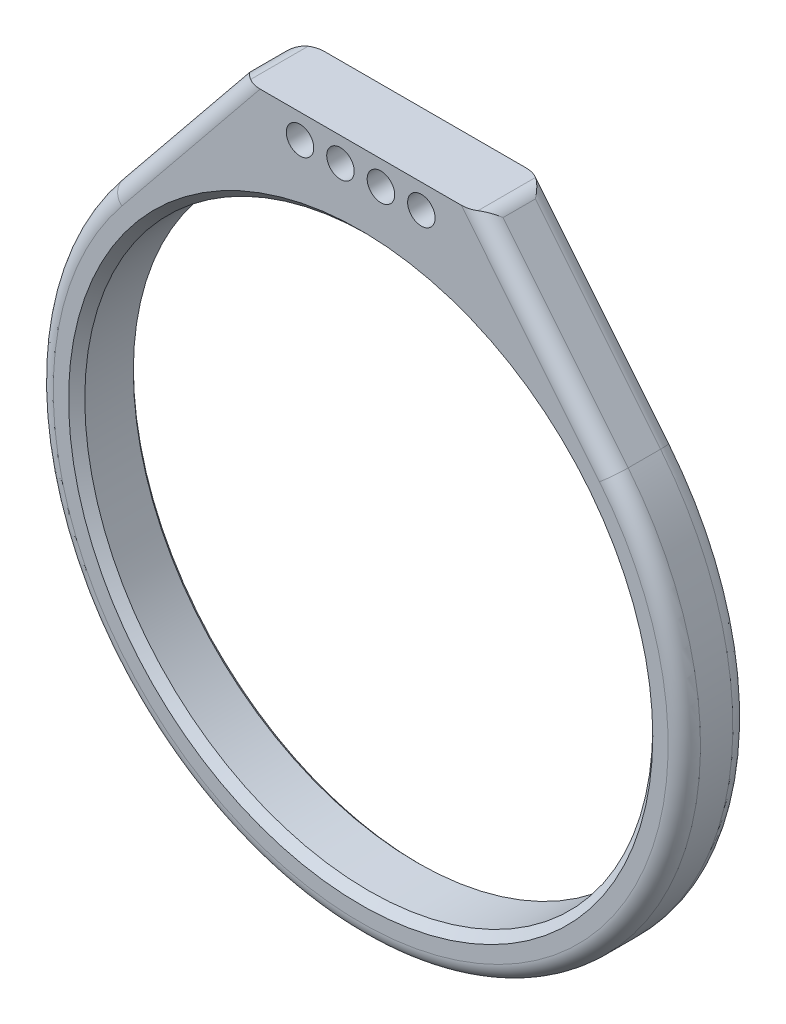
SolidWorks part; units mm, degrees
ref_plane "Front Plane" through (0, 0, 0) normal (0, 0, 1) x (1, 0, 0)
ref_plane "Top Plane" through (0, 0, 0) normal (0, 1, 0) x (1, 0, 0)
ref_plane "Right Plane" through (0, 0, 0) normal (1, 0, 0) x (0, 0, -1)
sketch "Sketch1" plane through (0, 0, 0) normal (0, 0, 1) x (1, 0, 0)
  line L0 (-15, 45) -> (0, 45)
  line L1 (0, 45) -> (15, 45)
  line L2 (-15, 45) -> (-31.0627, 25.2013)
  line L3 (15, 45) -> (31.0627, 25.2013)
  circle A0 centre (0, 0) radius 35.1
  arc A1 (-31.0627, 25.2013) -> (31.0627, 25.2013) centre (0, 0) ccw
  dimension "D1" = 70.2
  dimension "D2" = 80
  dimension "D3" = 15
  dimension "D4" = 15
  dimension "D5" = 45
extrude "Boss-Extrude1" add sketch "Sketch1" along normal blind 8
hole_wizard "M3 Clearance Hole1" positions "Sketch2" profile "Sketch3" hole size "M3" standard "GB"
sketch "Sketch2" plane through (0, 0, 8) normal (0, 0, 1) x (1, 0, 0)
  line L0 (15, 45) -> (-15, 45) construction
  line L1 (0, 45) -> (0, 39.1601) construction
  point P0 (7.5, 42)
  point P2 (-2.5, 42)
  point P15 (-7.5, 42)
  point P16 (2.5, 42)
  dimension "D1" = 7.5
  dimension "D2" = 10
  dimension "D3" = 3
sketch "Sketch3" plane through (7.5, 42, 8) normal (1, 0, 0) x (0, -1, 0)
  line L0 (0, 0) -> (0, 9.0215)
  line L1 (0, 9.0215) -> (1.7, 8)
  line L2 (1.7, 8) -> (1.7, 0)
  line L5 (1.7, 0) -> (0, 0)
  line L10 (0, 9.0215) -> (-1.7, 8) construction
  line L11 (0, -6.35) -> (0, 107.95) construction
  dimension "Hole Dia." = 3.4
  dimension "Hole Depth" = 8
  dimension "Drill Angle" = 118
chamfer "Chamfer1" distance 1 angle 45 2 edges at (35.1, 0, 8) (35.1, 0, 0)
fillet "Fillet1" radius 2 9 edges at (-23.0314, 35.1007, 8) (0, -40, 8) (-23.0314, 35.1007, 0) (0, -40, 0) (36.1, 0, 0) (23.0314, 35.1007, 8) (23.0314, 35.1007, 0) (-15, 45, 4) (15, 45, 4)
